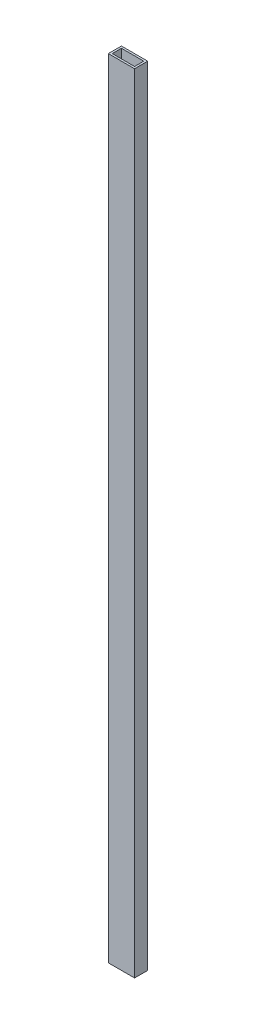
SolidWorks part; units mm, degrees
ref_plane "Спереди" through (0, 0, 0) normal (0, 0, 1) x (1, 0, 0)
ref_plane "Сверху" through (0, 0, 0) normal (0, 1, 0) x (1, 0, 0)
ref_plane "Справа" through (0, 0, 0) normal (1, 0, 0) x (0, 0, -1)
sketch "Эскиз1" plane through (0, 0, 0) normal (0, 1, 0) x (1, 0, 0)
  line L1 (-20, 10) -> (20, 10)
  line L2 (-20, 10) -> (-20, -10)
  line L3 (-20, -10) -> (20, -10)
  line L4 (20, 10) -> (20, -10)
  line L5 (-20, 10) -> (20, -10) construction
  line L6 (-20, -10) -> (20, 10) construction
  point P0 (0, 0)
  dimension "D1" = 40
  dimension "D2" = 20
extrude "Вытянуть-Тонкостенный1" add sketch "Эскиз1" along normal blind 1200 thin
